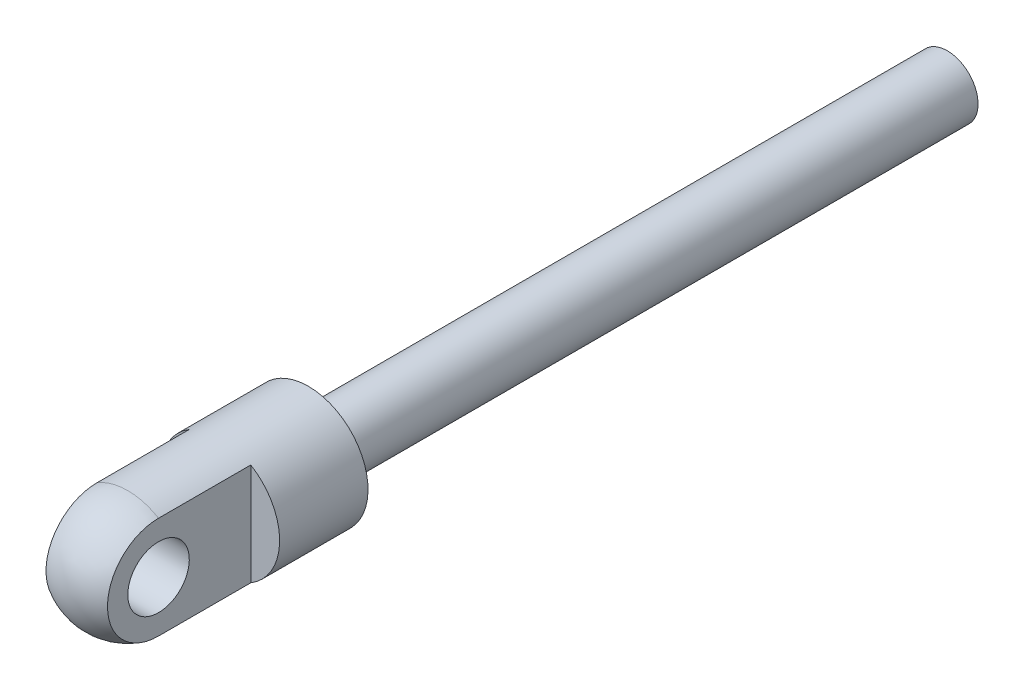
SolidWorks part; units mm, degrees
ref_plane "Front" through (0, 0, 0) normal (0, 0, 1) x (1, 0, 0)
ref_plane "Top" through (0, 0, 0) normal (0, 1, 0) x (1, 0, 0)
ref_plane "Right" through (0, 0, 0) normal (1, 0, 0) x (0, 0, -1)
sketch "Sketch1" plane through (0, 0, 0) normal (1, 0, 0) x (0, 0, -1)
  line L0 (-54.991, 0) -> (54.991, 0) construction
  line L1 (-54.991, 0) -> (-54.991, -0.254) construction
  line L2 (-25.019, 0) -> (-25.019, -0.254) construction
  line L3 (54.991, -0.254) -> (54.991, 0) construction
  line L4 (46.609, 0) -> (46.609, 5.969)
  line L5 (-13.0302, 2.0828) -> (-13.0302, 5.969)
  line L6 (-43.053, 0) -> (-43.053, 2.032) construction
  line L7 (-43.053, 2.032) -> (-13.0302, 2.032) construction
  line L8 (-13.0302, 5.969) -> (46.609, 5.969)
  line L11 (29.1846, 0) -> (46.609, 0)
  line L12 (-13.0302, 2.0828) -> (16.9926, 2.0828)
  line L13 (16.9926, 2.0828) -> (16.9926, 0) construction
  line L14 (16.9926, 2.0828) -> (29.1846, 2.0828)
  line L15 (29.1846, 2.0828) -> (29.1846, 0)
  line L16 (-13.0302, 2.0828) -> (-13.0302, 2.032) construction
  dimension "D4" = 8.382
  dimension "D5" = 11.938
  dimension "D6" = 11.9888
  dimension "E Cylinder Dia" = 11.938
  dimension "D Rod Dia" = 4.064
  dimension "D7" = 0.0508
  dimension "D8" = 12.192
  dimension "D9" = 3.8862
  dimension "D1" = 0.254
revolve "Revolve1" add sketch "Sketch1" angle 360 about L0
fillet "Fillet2" radius 0.7772 2 edges at (5.969, 0, -46.609) (5.969, 0, 13.0302)
sketch "Sketch2" plane through (0, 0, 0) normal (1, 0, 0) x (0, 0, -1)
  line L0 (46.609, 3.81) -> (54.991, 3.81)
  line L2 (46.609, -3.81) -> (46.609, 3.81)
  line L5 (46.609, 0) -> (46.609, 5.969) construction
  line L7 (46.609, -3.81) -> (54.991, -3.81)
  arc A0 (54.991, 3.81) -> (54.991, -3.81) centre (54.991, 0) cw
  circle A3 centre (54.991, 0) radius 2.032
  dimension "D4" = 4.064
  dimension "D1" = 7.62
extrude "Extrude2" add sketch "Sketch2" along normal mid plane 4.064
sketch "Sketch9" plane through (0, 0, 0) normal (1, 0, 0) x (0, 0, -1)
  line L0 (-43.053, 0) -> (-43.053, 2.032) construction
  line L2 (-43.053, 0) -> (-43.053, 2.032)
  line L3 (-43.053, 2.032) -> (-0.8382, 2.032)
  line L4 (-0.8382, 2.032) -> (-0.8382, 0)
  line L5 (-0.8382, 0) -> (-43.053, 0)
  line L6 (-43.053, 0) -> (-54.991, 0) construction
  line L8 (-0.8382, 1.016) -> (-13.0302, 1.016) construction
  line L9 (-13.0302, 1.016) -> (-13.0302, 2.032) construction
  line L10 (16.9926, 2.0828) -> (29.1846, 2.0828) construction
revolve "Revolve5" add sketch "Sketch9" angle 360 about L6
sketch "Sketch11" plane through (0, 0, 0) normal (1, 0, 0) x (0, 0, -1)
  line L0 (-43.053, 0) -> (-43.053, 3.937)
  line L1 (-43.053, 3.937) -> (-54.991, 3.937)
  line L2 (-58.928, 0) -> (-43.053, 0)
  line L3 (-58.928, 0) -> (-62.865, 0) construction
  line L4 (-54.991, 0) -> (54.991, 0) construction
  arc A0 (-54.991, 3.937) -> (-58.928, 0) centre (-54.991, 0) ccw
  circle A1 centre (-54.991, 0) radius 2.032 construction
  dimension "D2" = 4.064
  dimension "D1" = 7.874
revolve "Revolve6" add sketch "Sketch11" angle 360 about L3
sketch "Sketch12" plane through (0, 0, 0) normal (1, 0, 0) x (0, 0, -1)
  circle A0 centre (-54.991, 0) radius 2.032 construction
  circle A1 centre (-54.991, 0) radius 2.032
extrude "Cut-Extrude1" cut sketch "Sketch12" against normal through all and the other way through all
ref_plane "Plane1" through (0, 0, 54.991) normal (0, 0, 1) x (1, 0, 0)
sketch "Sketch13" plane through (0, 0, 54.991) normal (0, 0, 1) x (1, 0, 0)
  line L0 (-2.032, -3.937) -> (2.032, 3.937) construction
  line L1 (-2.032, 3.937) -> (2.032, 3.937)
  line L2 (-2.032, 3.937) -> (-2.032, -3.937)
  line L3 (-2.032, -3.937) -> (2.032, -3.937)
  line L4 (2.032, 3.937) -> (2.032, -3.937)
  dimension "D1" = 4.064
extrude "Cut-Extrude2" cut sketch "Sketch13" against normal blind 6.096 and the other way through all flip side to cut
pattern_linear "LPattern1" count 2 spacing 29.972 along (0, 0, -1) of bodies 137
sketch "Sketch10" plane through (0, 0, 0) normal (1, 0, 0) x (0, 0, -1)
  line L0 (-43.053, 2.032) -> (-13.0302, 2.032) construction
  line L2 (-43.053, -2.032) -> (-0.8382, -2.032) construction
  arc A0 (-28.3911, 2.032) -> (-28.3911, -2.032) centre (-25.019, 0) ccw
  arc A1 (-25.019, 3.937) -> (-25.019, -3.937) centre (-25.019, 0) ccw construction
delete or keep bodies "Body-Delete/Keep 1" type delete bodies bodies 137 134
equation "\"D1@Fillet2\"=\"D9@Sketch1\"/5"
equation "\"D3@LPattern1\"=\"C Stroke@Sketch1\""
